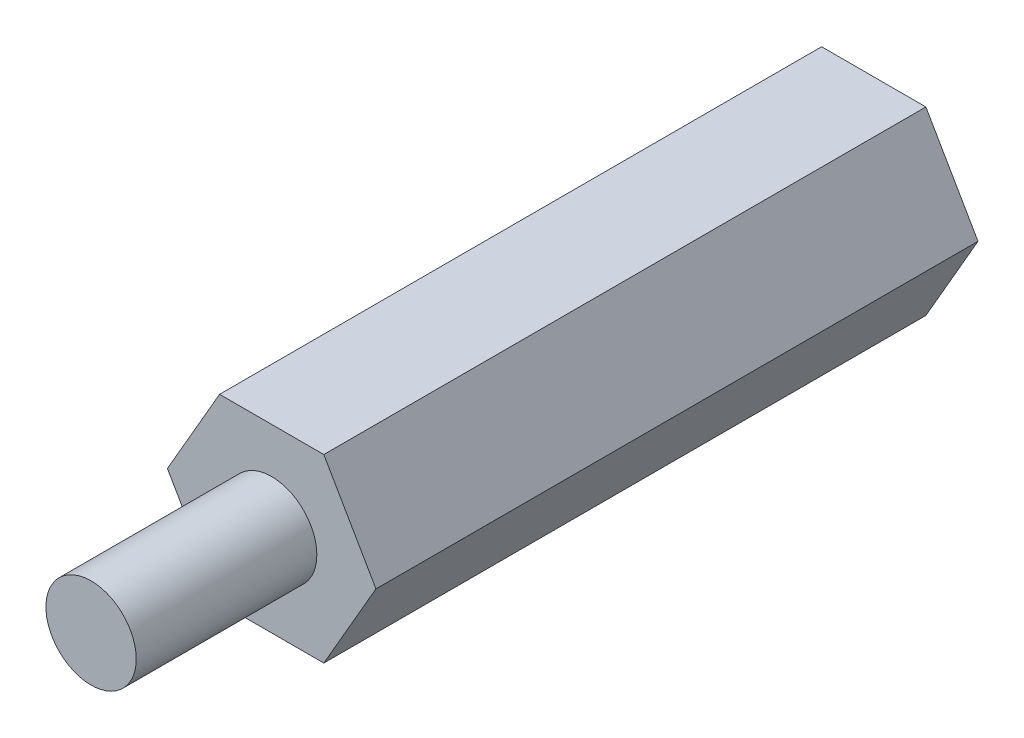
SolidWorks part; units mm, degrees
ref_plane "Front Plane" through (0, 0, 0) normal (0, 0, 1) x (1, 0, 0)
ref_plane "Top Plane" through (0, 0, 0) normal (0, 1, 0) x (1, 0, 0)
ref_plane "Right Plane" through (0, 0, 0) normal (1, 0, 0) x (0, 0, -1)
sketch "Sketch1" plane through (0, 0, 0) normal (0, 0, 1) x (1, 0, 0)
  line L1 (-3.4641, 0) -> (-1.7321, -3)
  line L2 (-1.7321, -3) -> (1.7321, -3)
  line L3 (1.7321, -3) -> (3.4641, 0)
  line L4 (3.4641, 0) -> (1.7321, 3)
  line L5 (1.7321, 3) -> (-1.7321, 3)
  line L6 (-1.7321, 3) -> (-3.4641, 0)
  circle A0 centre (0, 0) radius 3 construction
  dimension "D1" = 6
extrude "Boss-Extrude1" add sketch "Sketch1" along normal blind 20
sketch "Sketch2" plane through (0, 0, 20) normal (0, 0, 1) x (1, 0, 0)
  circle A0 centre (0, 0) radius 1.5
  dimension "D1" = 3
extrude "Boss-Extrude2" add sketch "Sketch2" along normal blind 6
cosmetic thread "Cosmetic Thread1" parameters "D1"=6, "D2"=2.439
hole_wizard "M3x0.5 Tapped Hole1" positions "Sketch4" profile "Sketch3" tap size "M3x0.5" standard "ANSI Metric"
sketch "Sketch4" plane through (0, 0, 0) normal (0, 0, -1) x (-1, 0, 0)
  point P0 (0, 0)
sketch "Sketch3" plane through (0, 0, 0) normal (1, 0, 0) x (0, 1, 0)
  line L0 (0, 0) -> (0, 6.7511)
  line L1 (0, 6.7511) -> (1.25, 6)
  line L2 (1.25, 6) -> (1.25, 0)
  line L5 (1.25, 0) -> (0, 0)
  line L10 (0, 6.7511) -> (-1.25, 6) construction
  line L11 (0, -6.35) -> (0, 107.95) construction
  dimension "Tap Drill Dia." = 2.5
  dimension "Tap Drill Depth" = 6
  dimension "Drill Angle" = 118
cosmetic thread "Hole Thread1" parameters "D1"=6, "D2"=3
